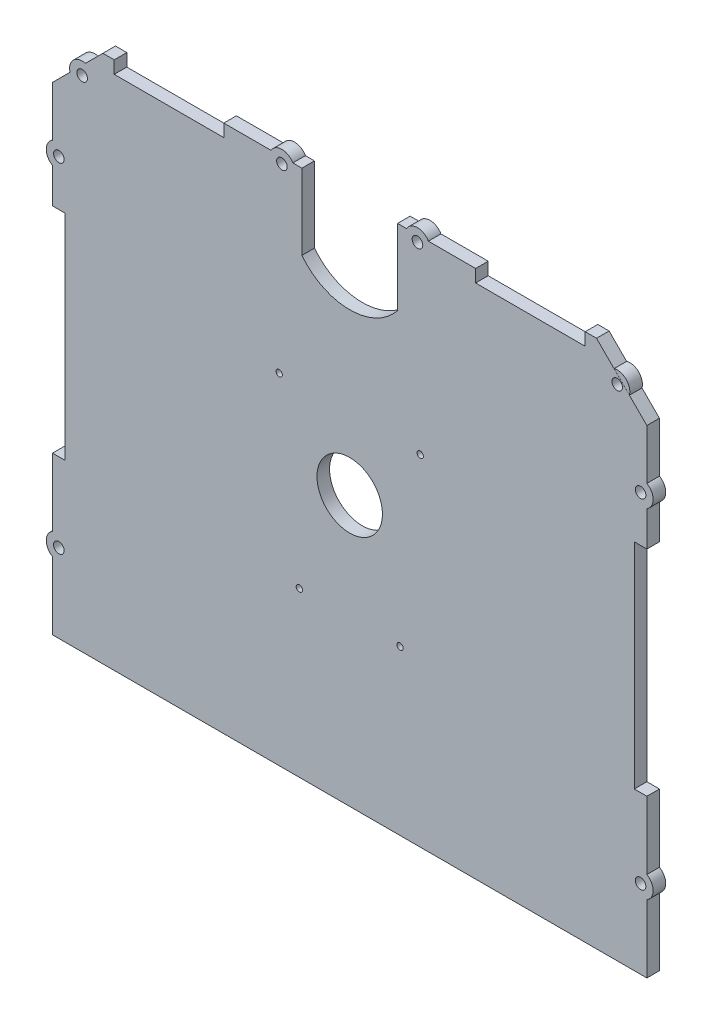
SolidWorks part; units mm, degrees
ref_plane "Front Plane" through (0, 0, 0) normal (0, 0, 1) x (1, 0, 0)
ref_plane "Top Plane" through (0, 0, 0) normal (0, 1, 0) x (1, 0, 0)
ref_plane "Right Plane" through (0, 0, 0) normal (1, 0, 0) x (0, 0, -1)
sketch "Sketch1" plane through (0, 0, 0) normal (0, 0, 1) x (1, 0, 0)
  line L0 (64.2262, -107) -> (118, -107)
  line L1 (-98, 103) -> (98, 103)
  line L3 (-118, -107) -> (-64.2262, -107)
  line L5 (-150, 100) -> (150, -100) construction
  line L6 (-150, -100) -> (150, 100) construction
  line L10 (0, 0) -> (0, 48.5738) construction
  line L12 (-47.5, 0) -> (47.5, 0) construction
  line L21 (78, 0) -> (118, 0) construction
  line L22 (118, 83) -> (118, -107)
  line L23 (-118, 83) -> (-118, -107)
  line L24 (-98, 103) -> (-98, 83) construction
  line L25 (-98, 83) -> (-118, 83) construction
  line L26 (0, 103) -> (0, -97) construction
  line L27 (-118, 83) -> (-98, 103)
  line L28 (98, 103) -> (118, 83)
  line L29 (-64.2262, -107) -> (64.2262, -107)
  point P0 (0, 0)
  point P19 (0, 0)
  point P22 (47.5, 0)
  point P33 (118, 0)
  dimension "D1" = 210
  dimension "D4" = 20
  dimension "D5" = 20
  dimension "D6" = 95
  dimension "D9" = 40
extrude "Boss-Extrude1" add sketch "Sketch1" along normal blind 5
sketch "Sketch4" plane through (0, 0, 5) normal (0, 0, 1) x (1, 0, 0)
  line L0 (-118, -2) -> (-113, -2) construction
  line L1 (-118, 83) -> (-118, -107) construction
  line L2 (-113, 40.5) -> (-113, -44.5)
  line L3 (-113, 40.5) -> (-118, 40.5)
  line L4 (-118, 40.5) -> (-118, -44.5)
  line L5 (-118, -44.5) -> (-113, -44.5)
  line L6 (0, 103) -> (0, 94.0884) construction
  line L7 (98, 103) -> (-98, 103) construction
  line L8 (118, -2) -> (113, -2) construction
  line L9 (118, -44.5) -> (113, -44.5)
  line L10 (118, 40.5) -> (118, -44.5)
  line L11 (113, 40.5) -> (118, 40.5)
  line L12 (113, 40.5) -> (113, -44.5)
  point P7 (-113, -2)
  point P20 (113, -2)
  dimension "D1" = 5
  dimension "D2" = 85
extrude "Cut-Extrude3" cut sketch "Sketch4" against normal through all
sketch "Sketch5" plane through (0, 0, 5) normal (0, 0, 1) x (1, 0, 0)
  line L0 (0, 103) -> (0, 98) construction
  line L1 (98, 103) -> (-98, 103) construction
  line L2 (0, 98) -> (50, 98) construction
  line L3 (-93.5, 98) -> (-50, 98) construction
  line L4 (-93.5, 103) -> (-50, 98) construction
  line L5 (93.5, 98) -> (50, 98)
  line L6 (93.5, 98) -> (93.5, 103)
  line L7 (93.5, 103) -> (50, 103)
  line L8 (50, 98) -> (50, 103)
  line L9 (93.5, 98) -> (50, 103) construction
  line L10 (93.5, 103) -> (50, 98) construction
  line L11 (-93.5, 98) -> (-50, 103) construction
  line L12 (-50, 98) -> (-50, 103)
  line L13 (-93.5, 103) -> (-50, 103)
  line L14 (-93.5, 98) -> (-93.5, 103)
  line L15 (-93.5, 98) -> (-50, 98)
  point P11 (71.75, 100.5)
  point P17 (-71.75, 100.5)
  dimension "D1" = 50
extrude "Cut-Extrude4" cut sketch "Sketch5" against normal blind 5
sketch "Sketch6" plane through (0, 0, 5) normal (0, 0, 1) x (1, 0, 0)
  line L0 (-50, 100.5) -> (-26.91, 100.5) construction
  line L2 (-50, 98) -> (-50, 103) construction
  line L3 (0, 103) -> (0, 83.4506) construction
  line L4 (50, 103) -> (-50, 103) construction
  circle A2 centre (-106.233, 91.2315) radius 2.1
  circle A3 centre (106.233, 91.2315) radius 2.1
  circle A4 centre (115.5, 58.75) radius 2.1
  circle A5 centre (115.5, -75.75) radius 2.1
  circle A6 centre (-115.5, 58.75) radius 2.1
  circle A7 centre (-115.5, -75.75) radius 2.1
  circle A8 centre (-26.91, 100.5) radius 2.1
  circle A9 centre (26.91, 100.5) radius 2.1
  dimension "D1" = 23.09
  dimension "D2" = 4.2
extrude "Cut-Extrude5" cut sketch "Sketch6" against normal blind 5
sketch "Sketch7" plane through (0, 0, 5) normal (0, 0, 1) x (1, 0, 0)
  line L0 (-104.9389, 96.0611) -> (-111.0626, 89.9374)
  line L1 (-118, 63.0801) -> (-118, 54.4199)
  line L2 (-118, -71.4199) -> (-118, -80.0801)
  line L3 (118, -71.4199) -> (118, -80.0801)
  line L4 (111.0626, 89.9374) -> (104.9992, 96.0769)
  line L5 (118, 54.4199) -> (118, 63.0801)
  line L9 (22.5799, 103) -> (31.2401, 103)
  line L10 (50, 103) -> (-50, 103) construction
  line L11 (-31.2401, 103) -> (-22.5799, 103)
  arc A0 (-118, 63.0801) -> (-118, 54.4199) centre (-115.5, 58.75) ccw construction
  arc A1 (-118, -71.4199) -> (-118, -80.0801) centre (-115.5, -75.75) ccw construction
  arc A2 (118, -80.0801) -> (118, -71.4199) centre (115.5, -75.75) ccw construction
  arc A3 (118, 54.4199) -> (118, 63.0801) centre (115.5, 58.75) ccw construction
  arc A4 (111.0626, 89.9374) -> (104.9992, 96.0769) centre (106.233, 91.2315) ccw construction
  arc A5 (-118, 63.0801) -> (-118, 54.4199) centre (-115.5, 58.75) ccw
  arc A6 (-118, -71.4199) -> (-118, -80.0801) centre (-115.5, -75.75) ccw
  arc A7 (118, -80.0801) -> (118, -71.4199) centre (115.5, -75.75) ccw
  arc A8 (118, 54.4199) -> (118, 63.0801) centre (115.5, 58.75) ccw
  arc A9 (111.0626, 89.9374) -> (104.9992, 96.0769) centre (106.233, 91.2315) ccw
  arc A10 (-104.9389, 96.0611) -> (-111.0626, 89.9374) centre (-106.233, 91.2315) ccw construction
  arc A11 (-104.9389, 96.0611) -> (-111.0626, 89.9374) centre (-106.233, 91.2315) ccw
  arc A14 (31.2401, 103) -> (22.5799, 103) centre (26.91, 100.5) ccw
  arc A15 (-22.5799, 103) -> (-31.2401, 103) centre (-26.91, 100.5) ccw
  dimension "D1" = 10
  dimension "D2" = 10
extrude "Boss-Extrude2" add sketch "Sketch7" against normal blind 5
sketch "Sketch8" plane through (0, 0, 5) normal (0, 0, 1) x (1, 0, 0)
  circle A0 centre (0, 0) radius 13
  dimension "D1" = 26
extrude "Cut-Extrude6" cut sketch "Sketch8" against normal blind 5
sketch "Sketch9" plane through (0, 0, 5) normal (0, 0, 1) x (1, 0, 0)
  circle A4 centre (28, 28) radius 1.25
  circle A5 centre (20, -42) radius 1.25
  circle A6 centre (-20, -42) radius 1.25
  circle A7 centre (-28, 28) radius 1.25
extrude "Cut-Extrude7" cut sketch "Sketch9" against normal blind 5
sketch "Sketch10" plane through (0, 0, 5) normal (0, 0, 1) x (1, 0, 0)
  line L0 (0, 103) -> (0, 73) construction
  line L2 (19, 103) -> (19, 73)
  line L3 (-19, 103) -> (-19, 73)
  arc A0 (-19, 73) -> (19, 73) centre (0, 88) ccw
  point P2 (0, 0)
  point P10 (0, 0)
  point P11 (0, 0)
  dimension "D1" = 30
  dimension "D2" = 19
  dimension "D3" = 30
extrude "Cut-Extrude8" cut sketch "Sketch10" against normal blind 5 and the other way through all
